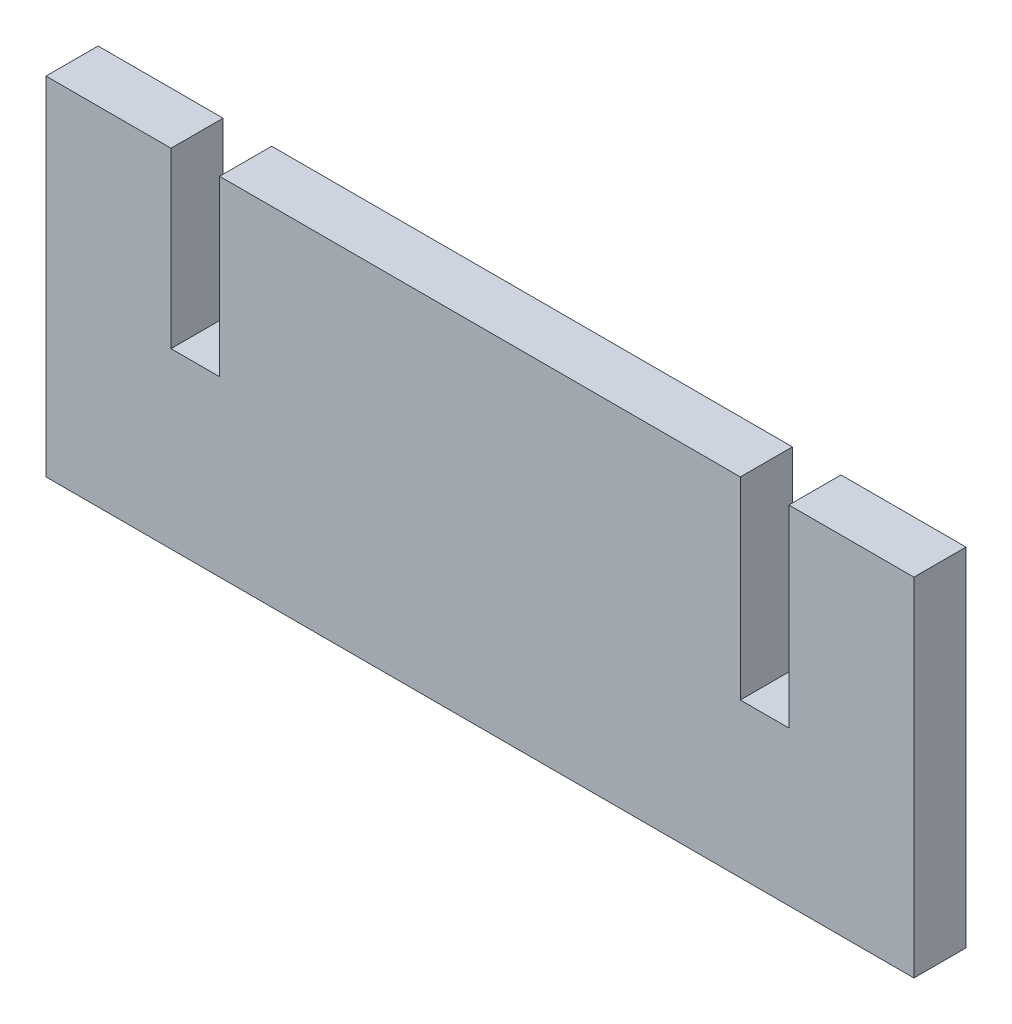
SolidWorks part; units mm, degrees
ref_plane "Plan de face" through (0, 0, 0) normal (0, 0, 1) x (1, 0, 0)
ref_plane "Plan de dessus" through (0, 0, 0) normal (0, 1, 0) x (1, 0, 0)
ref_plane "Plan de droite" through (0, 0, 0) normal (1, 0, 0) x (0, 0, -1)
sketch "Esquisse1" plane through (0, 0, 0) normal (0, 0, 1) x (1, 0, 0)
  line L0 (10, 20) -> (40, 20)
  line L1 (0, 0) -> (50, 0)
  line L2 (0, 0) -> (0, 20)
  line L3 (0, 20) -> (7.2, 20)
  line L4 (50, 0) -> (50, 20)
  line L6 (7.2, 20) -> (7.2, 10)
  line L7 (7.2, 10) -> (10, 10)
  line L8 (10, 20) -> (10, 10)
  line L10 (40, 20) -> (40, 8.8698)
  line L11 (40, 8.8698) -> (42.8, 8.8698)
  line L12 (42.8, 20) -> (42.8, 8.8698)
  line L13 (42.8, 20) -> (50, 20)
  dimension "D1" = 2.8
  dimension "D2" = 10
  dimension "D3" = 20
  dimension "D4" = 2.8
  dimension "D5" = 30
  dimension "D6" = 50
  dimension "D7" = 10
extrude "Boss.-Extru.1" add sketch "Esquisse1" along normal blind 3
